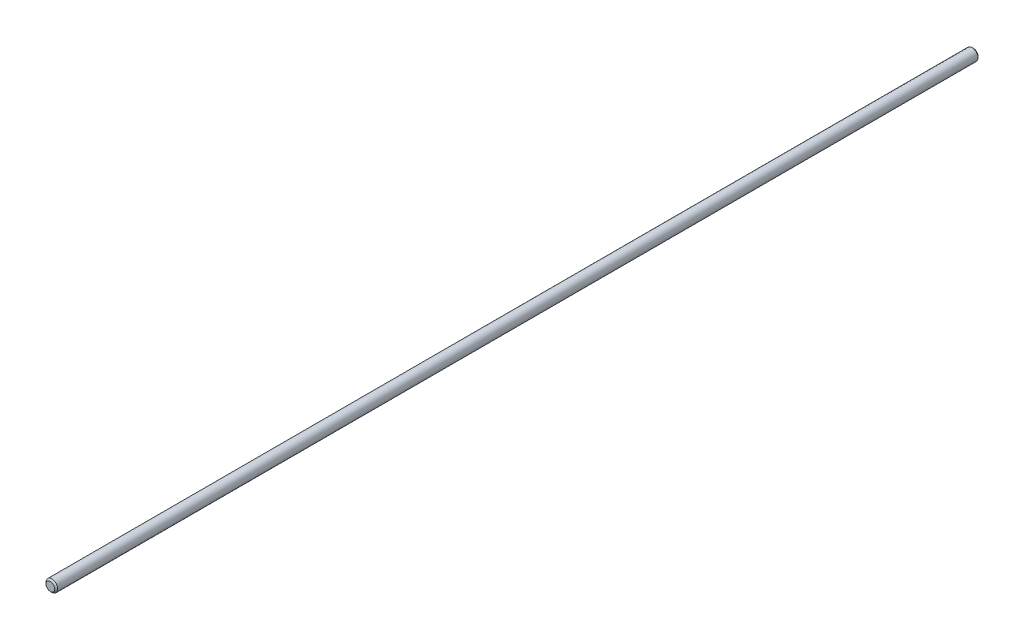
SolidWorks part; units mm, degrees
ref_plane "Front Plane" through (0, 0, 0) normal (0, 0, 1) x (1, 0, 0)
ref_plane "Top Plane" through (0, 0, 0) normal (0, 1, 0) x (1, 0, 0)
ref_plane "Right Plane" through (0, 0, 0) normal (1, 0, 0) x (0, 0, -1)
sketch "Sketch1" plane through (0, 0, 0) normal (0, 0, 1) x (1, 0, 0)
  circle A0 centre (0, 0) radius 4
  dimension "D1" = 8
extrude "Boss-Extrude1" add sketch "Sketch1" along normal blind 630
chamfer "Chamfer1" distance 1 angle 45 2 edges at (4, 0, 630) (4, 0, 0)
